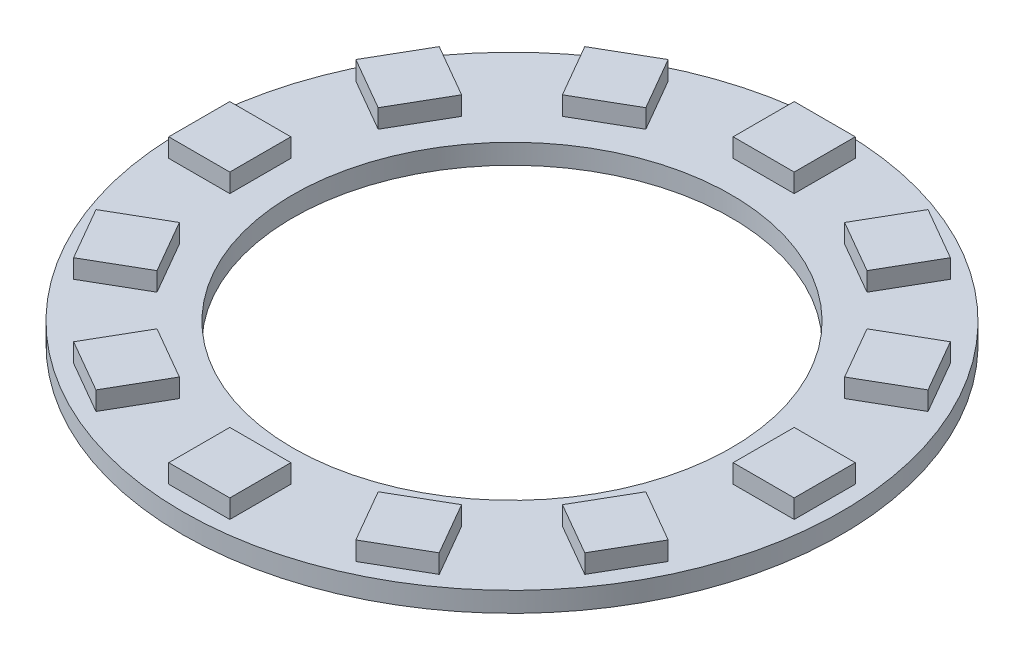
SolidWorks part; units mm, degrees
ref_plane "前视基准面" through (0, 0, 0) normal (0, 0, 1) x (1, 0, 0)
ref_plane "上视基准面" through (0, 0, 0) normal (0, 1, 0) x (1, 0, 0)
ref_plane "右视基准面" through (0, 0, 0) normal (1, 0, 0) x (0, 0, -1)
sketch "草图1" plane through (0, 0, 0) normal (0, 1, 0) x (1, 0, 0)
  circle A0 centre (0, 0) radius 26.45
  circle A1 centre (0, 0) radius 17.6
  dimension "D1" = 52.9
  dimension "D2" = 35.2
extrude "凸台-拉伸1" add sketch "草图1" along normal blind 1.6
sketch "草图2" plane through (0, 1.6, 0) normal (0, 1, 0) x (1, 0, 0)
  line L1 (-25.1, -2.45) -> (-20.2, -2.45)
  line L2 (-25.1, -2.45) -> (-25.1, 2.45)
  line L3 (-25.1, 2.45) -> (-20.2, 2.45)
  line L4 (-20.2, -2.45) -> (-20.2, 2.45)
  line L5 (-25.1, -2.45) -> (-20.2, 2.45) construction
  line L6 (-25.1, 2.45) -> (-20.2, -2.45) construction
  circle A0 centre (0, 0) radius 25.1 construction
  point P0 (-22.65, 0)
  point P7 (-20.8624, 0)
  dimension "D1" = 50.2
  dimension "D2" = 4.9
  dimension "D3" = 4.9
extrude "凸台-拉伸2" add sketch "草图2" along normal blind 1.5
pattern_circular "阵列(圆周)1" count 12 over 360 about axis through (0, 0, 0) along (0, 1, 0) of "凸台-拉伸2"
